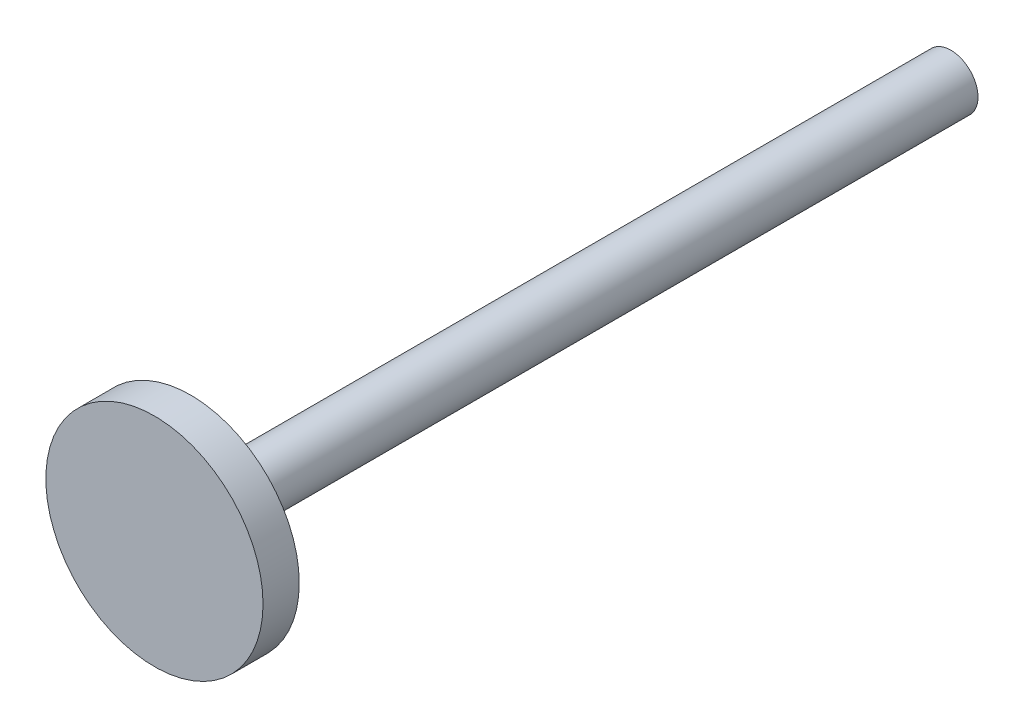
SolidWorks part; units mm, degrees
ref_plane "Front Plane" through (0, 0, 0) normal (0, 0, 1) x (1, 0, 0)
ref_plane "Top Plane" through (0, 0, 0) normal (0, 1, 0) x (1, 0, 0)
ref_plane "Right Plane" through (0, 0, 0) normal (1, 0, 0) x (0, 0, -1)
sketch "Sketch1" plane through (0, 0, 0) normal (0, 0, 1) x (1, 0, 0)
  circle A0 centre (0, 0) radius 9.525
  dimension "D1" = 19.05
extrude "Boss-Extrude1" add sketch "Sketch1" along normal blind 279.4
sketch "Sketch2" plane through (0, 0, 279.4) normal (0, 0, 1) x (1, 0, 0)
  circle A0 centre (0, 0) radius 38.1
  dimension "D1" = 76.2
extrude "Boss-Extrude2" add sketch "Sketch2" against normal blind 12.7
